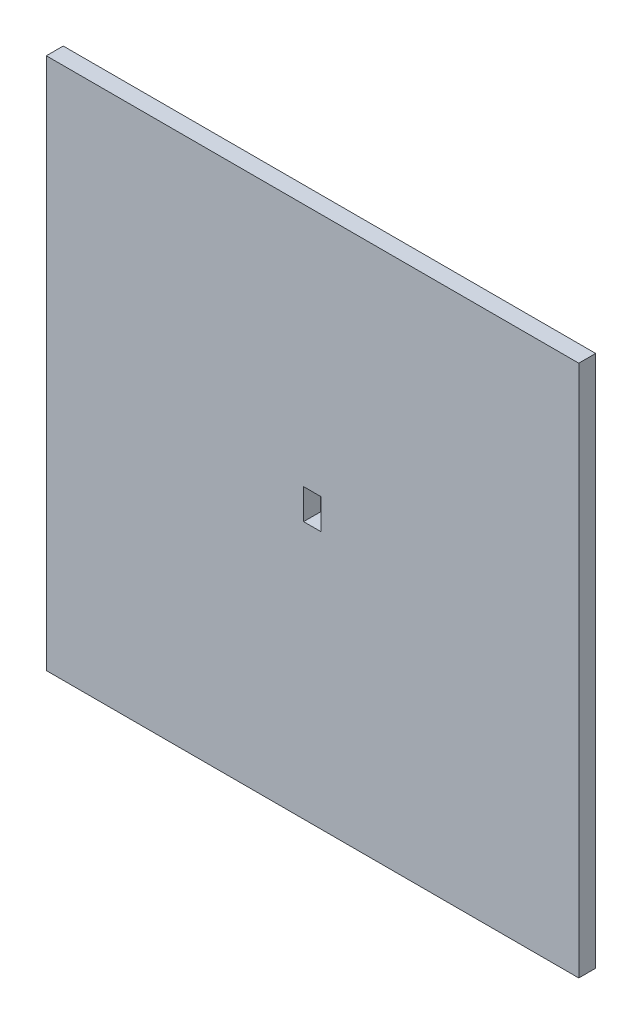
SolidWorks part; units mm, degrees
ref_plane "Front Plane" through (0, 0, 0) normal (0, 0, 1) x (1, 0, 0)
ref_plane "Top Plane" through (0, 0, 0) normal (0, 1, 0) x (1, 0, 0)
ref_plane "Right Plane" through (0, 0, 0) normal (1, 0, 0) x (0, 0, -1)
sketch "Sketch1" plane through (0, 0, 0) normal (0, 0, 1) x (1, 0, 0)
  line L1 (0, 0) -> (100, 0)
  line L2 (0, 0) -> (0, 100)
  line L3 (0, 100) -> (100, 100)
  line L4 (100, 0) -> (100, 100)
  dimension "D1" = 100
  dimension "D2" = 100
extrude "Boss-Extrude1" add sketch "Sketch1" along normal blind 3.175
sketch "Sketch3" plane through (0, 0, 3.175) normal (0, 0, 1) x (1, 0, 0)
  line L0 (0, 100) -> (100, 0) construction
  line L1 (0, 0) -> (100, 100) construction
  line L2 (49.9664, 54.0836) -> (49.9664, 48.3836) construction
  line L3 (48.3164, 54.0836) -> (51.6164, 54.0836)
  line L4 (48.3164, 54.0836) -> (48.3164, 48.3836)
  line L5 (48.3164, 48.3836) -> (51.6164, 48.3836)
  line L6 (51.6164, 54.0836) -> (51.6164, 48.3836)
  line L8 (48.3164, 51.2336) -> (51.6164, 51.2336) construction
  dimension "D1" = 5.7
  dimension "D2" = 3.3
extrude "Cut-Extrude1" cut sketch "Sketch3" against normal through all
sketch "Sketch4" plane through (0, 0, 3.175) normal (0, 0, 1) x (1, 0, 0)
  line L0 (48.3164, 54.0836) -> (48.3164, 48.3836) construction
  line L1 (44.7664, 53.777) -> (46.5664, 53.777)
  line L2 (44.7664, 53.777) -> (44.7664, 48.3157)
  line L3 (44.7664, 48.3157) -> (46.5664, 48.3157)
  line L4 (46.5664, 53.777) -> (46.5664, 48.3157)
  dimension "D1" = 1.75
  dimension "D2" = 1.8
